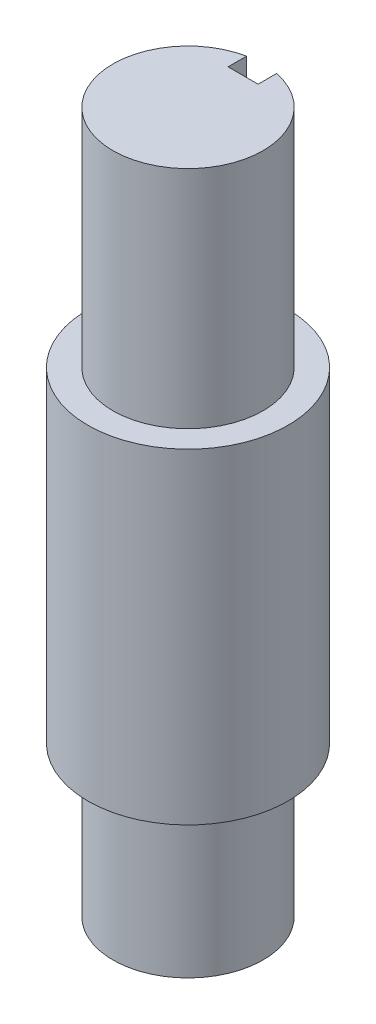
SolidWorks part; units mm, degrees
ref_plane "Front Plane" through (0, 0, 0) normal (0, 0, 1) x (1, 0, 0)
ref_plane "Top Plane" through (0, 0, 0) normal (0, 1, 0) x (1, 0, 0)
ref_plane "Right Plane" through (0, 0, 0) normal (1, 0, 0) x (0, 0, -1)
sketch "Sketch1" plane through (0, 0, 0) normal (0, 1, 0) x (1, 0, 0)
  circle A0 centre (0, 0) radius 20
  dimension "D1" = 40
extrude "Boss-Extrude1" add sketch "Sketch1" along normal mid plane 80
sketch "Sketch2" plane through (0, 40, 0) normal (0, 1, 0) x (1, 0, 0)
  circle A0 centre (0, 0) radius 15
  dimension "D1" = 30
extrude "Boss-Extrude2" add sketch "Sketch2" along normal blind 30
sketch "Sketch3" plane through (0, -40, 0) normal (0, -1, 0) x (1, 0, 0)
  circle A1 centre (0, 0) radius 15
  circle A2 centre (0, 0) radius 15
  dimension "D1" = 0
extrude "Boss-Extrude3" add sketch "Sketch3" along normal blind 30
sketch "Sketch4" plane through (0, 40, 0) normal (0, 1, 0) x (1, 0, 0)
  circle A0 centre (0, 0) radius 20 construction
  circle A1 centre (0, 0) radius 20
  circle A2 centre (0, 0) radius 15 construction
  circle A3 centre (0, 0) radius 15
extrude "Cut-Extrude1" cut sketch "Sketch4" against normal blind 15
sketch "Sketch5" plane through (0, 70, 0) normal (0, 1, 0) x (1, 0, 0)
  line L0 (0, 0) -> (0, 15) construction
  line L2 (-3, 19) -> (3, 19)
  line L3 (-3, 19) -> (-3, 11)
  line L4 (-3, 11) -> (3, 11)
  line L5 (3, 19) -> (3, 11)
  line L6 (0, 11) -> (0, 19) construction
  line L7 (-3, 15) -> (3, 15) construction
  circle A0 centre (0, 0) radius 15 construction
  dimension "D1" = 8
  dimension "D2" = 6
extrude "Cut-Extrude2" cut sketch "Sketch5" against normal up to surface (45 mm away) up to face at (0, 25, 15)
